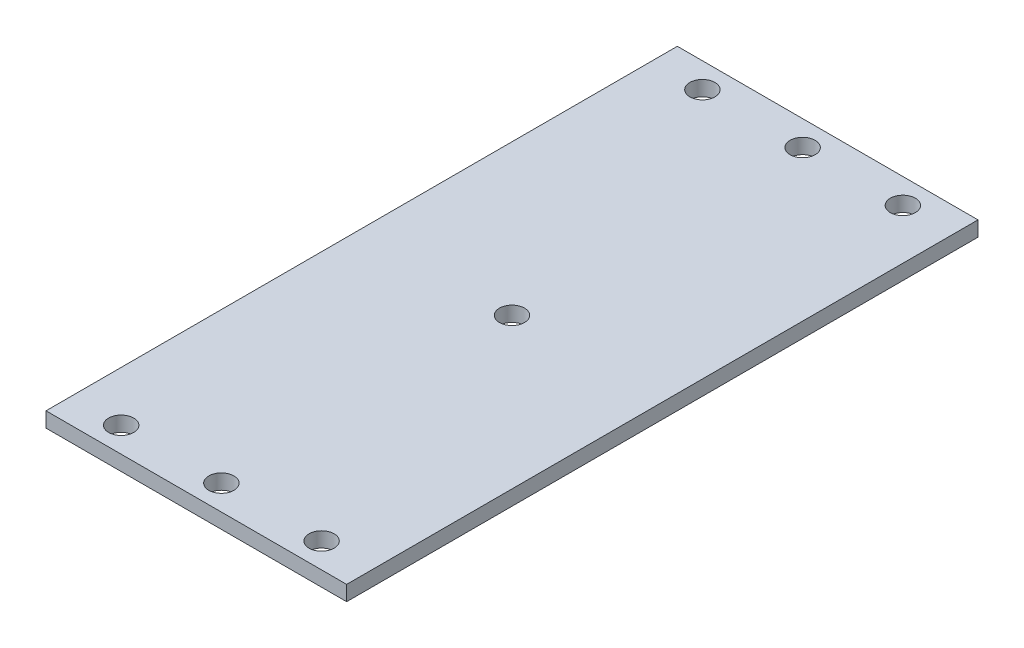
SolidWorks part; units mm, degrees
ref_plane "Front Plane" through (0, 0, 0) normal (0, 0, 1) x (1, 0, 0)
ref_plane "Top Plane" through (0, 0, 0) normal (0, 1, 0) x (1, 0, 0)
ref_plane "Right Plane" through (0, 0, 0) normal (1, 0, 0) x (0, 0, -1)
sketch "Sketch1" plane through (0, 0, 0) normal (0, 1, 0) x (1, 0, 0)
  line L1 (-30, 63) -> (30, 63)
  line L2 (-30, 63) -> (-30, -63)
  line L3 (-30, -63) -> (30, -63)
  line L4 (30, 63) -> (30, -63)
  line L5 (-30, 63) -> (30, -63) construction
  line L6 (-30, -63) -> (30, 63) construction
  point P0 (0, 0)
  dimension "D1" = 126
  dimension "D2" = 60
extrude "Boss-Extrude1" add sketch "Sketch1" along normal blind 3
sketch "Sketch2" plane through (0, 3, 0) normal (0, 1, 0) x (1, 0, 0)
  line L0 (-30, -63) -> (30, -63) construction
  line L1 (-30, 0) -> (30, 0) construction
  line L2 (-30, 63) -> (-30, -63) construction
  line L3 (30, -63) -> (30, 63) construction
  circle A0 centre (0, -58) radius 2.5
  circle A1 centre (20, -58) radius 2.5
  circle A2 centre (-20, -58) radius 2.5
  circle A3 centre (20, 58) radius 2.5
  circle A4 centre (0, 58) radius 2.5
  circle A5 centre (-20, 58) radius 2.5
  circle A6 centre (0, 0) radius 2.5
  point P8 (0, -63)
  dimension "D1" = 5
  dimension "D2" = 5
  dimension "D3" = 5
  dimension "D4" = 20
  dimension "D5" = 20
  dimension "D6" = 0
extrude "Cut-Extrude1" cut sketch "Sketch2" against normal blind 5
